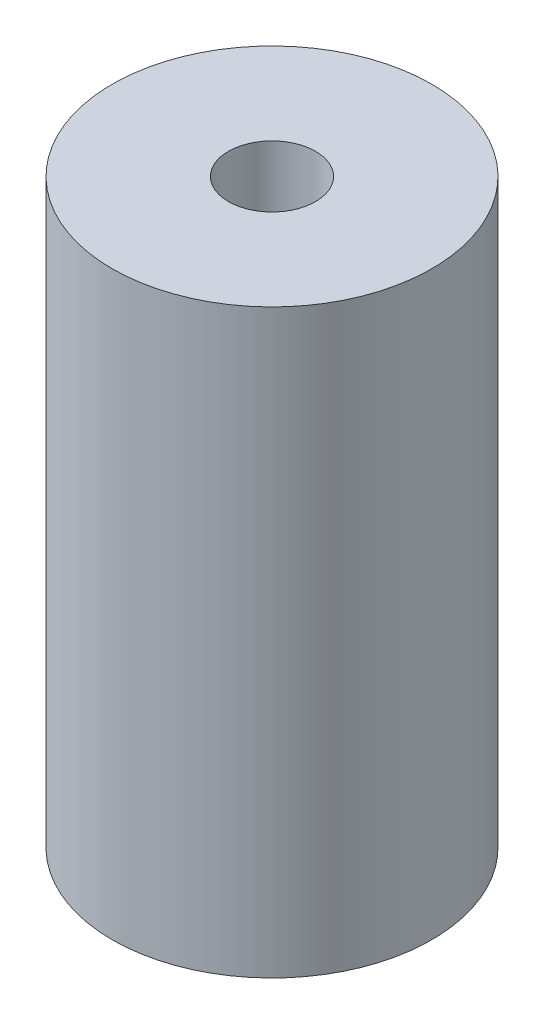
SolidWorks part; units mm, degrees
ref_plane "Front Plane" through (0, 0, 0) normal (0, 0, 1) x (1, 0, 0)
ref_plane "Top Plane" through (0, 0, 0) normal (0, 1, 0) x (1, 0, 0)
ref_plane "Right Plane" through (0, 0, 0) normal (1, 0, 0) x (0, 0, -1)
sketch "Sketch1" plane through (0, 0, 0) normal (0, 1, 0) x (1, 0, 0)
  circle A0 centre (0, 0) radius 1.5
  circle A1 centre (0, 0) radius 5.5
  dimension "D1" = 3
  dimension "D2" = 4
extrude "Boss-Extrude1" add sketch "Sketch1" along normal blind 20
